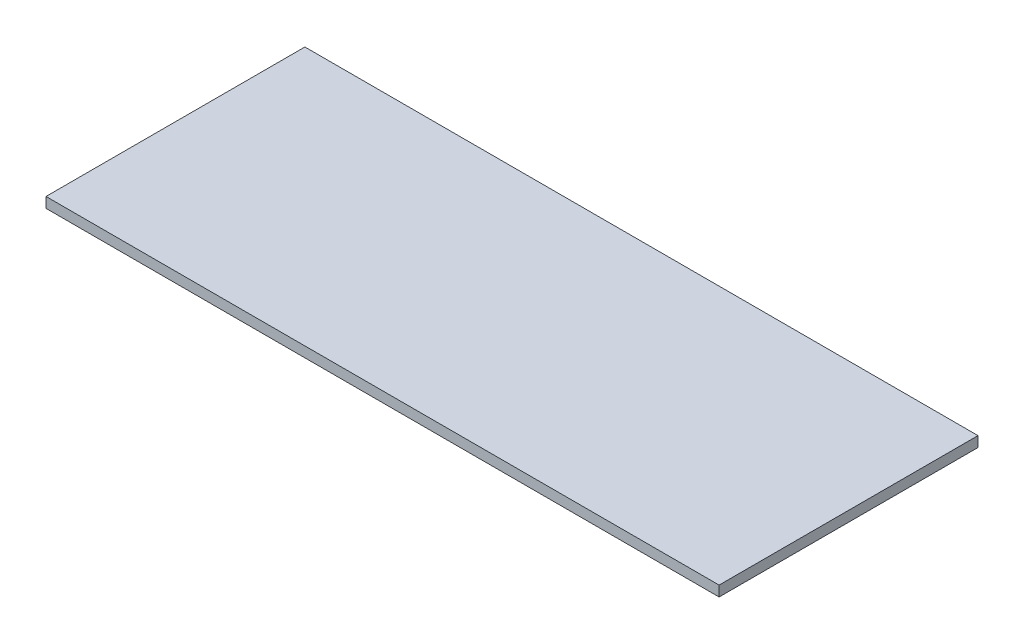
SolidWorks part; units mm, degrees
ref_plane "Front Plane" through (0, 0, 0) normal (0, 0, 1) x (1, 0, 0)
ref_plane "Top Plane" through (0, 0, 0) normal (0, 1, 0) x (1, 0, 0)
ref_plane "Right Plane" through (0, 0, 0) normal (1, 0, 0) x (0, 0, -1)
sketch "Sketch1" plane through (0, 0, 0) normal (0, 1, 0) x (1, 0, 0)
  line L1 (-260, 100) -> (260, 100)
  line L2 (-260, 100) -> (-260, -100)
  line L3 (-260, -100) -> (260, -100)
  line L4 (260, 100) -> (260, -100)
  line L5 (-260, 100) -> (260, -100) construction
  line L6 (-260, -100) -> (260, 100) construction
  point P0 (0, 0)
  dimension "D1" = 520
  dimension "D2" = 200
extrude "Boss-Extrude1" add sketch "Sketch1" along normal blind 8
